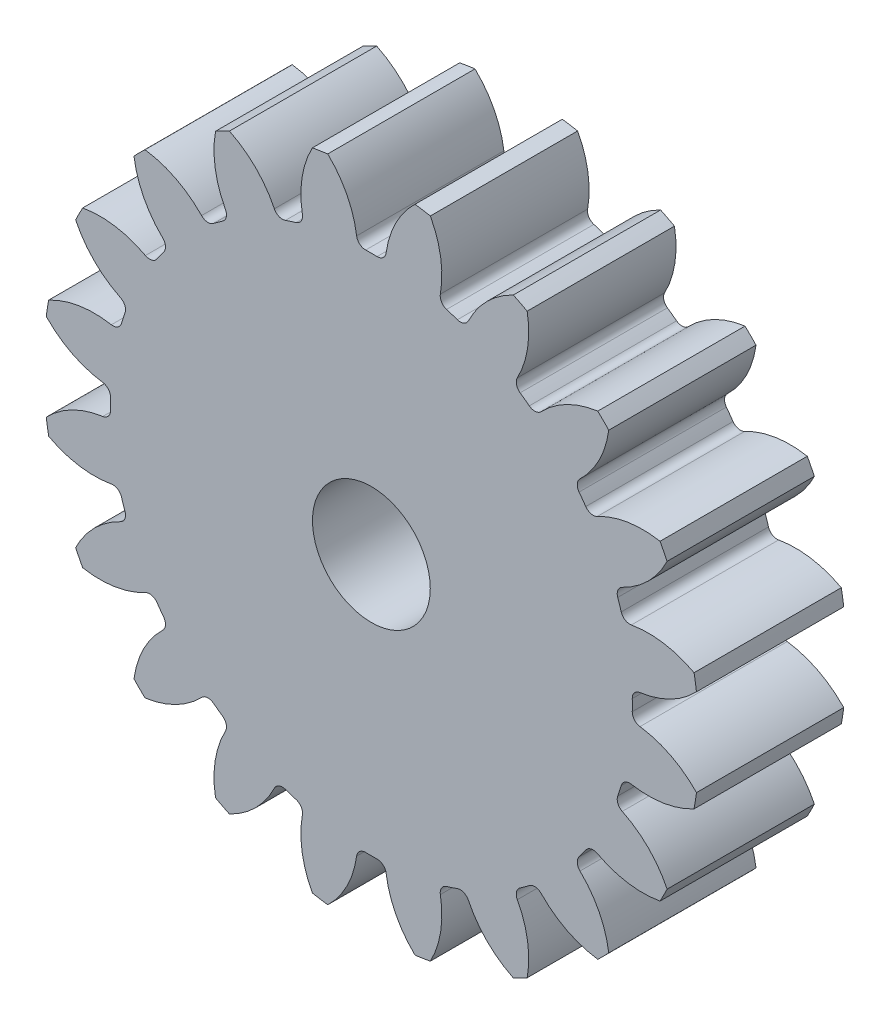
SolidWorks part; units mm, degrees
material "Custom Plastic"
ref_plane "Front Plane" through (0, 0, 0) normal (0, 0, 1) x (1, 0, 0)
ref_plane "Top Plane" through (0, 0, 0) normal (0, 1, 0) x (1, 0, 0)
ref_plane "Right Plane" through (0, 0, 0) normal (1, 0, 0) x (0, 0, -1)
sketch "Sketch1" plane through (0, 0, 0) normal (0, 0, 1) x (1, 0, 0)
  circle A0 centre (0, 0) radius 20.25
  circle A1 centre (0, 0) radius 22.275
  circle A2 centre (0, 0) radius 17.7188
  dimension "D1" = 40.5
  dimension "D3" = 35.4375
  dimension "D2" = 2.025
extrude "Boss-Extrude1" add sketch "Sketch1" along normal blind 10 contours A1
sketch "Sketch2" plane through (0, 0, 0) normal (0, 0, 1) x (1, 0, 0)
  line L0 (0, 0) -> (0, 22.275) construction
  line L1 (-1.5888, 20.1876) -> (1.5888, 20.1876) construction
  line L2 (-0.9484, 17.6934) -> (0, 0) construction
  line L3 (-2.3243, 22.3042) -> (0, 15.9182) construction
  line L4 (0, 0) -> (3.4846, 22.0008) construction
  line L5 (1.5888, 20.1876) -> (4.7273, 19.6905) construction
  circle A0 centre (0, 0) radius 22.275 construction
  arc A1 (-3.1037, 22.2092) -> (-0.9484, 17.6934) centre (-7.4915, 17.3426) cw
  arc A2 (3.1037, 22.2092) -> (0.9484, 17.6934) centre (7.4915, 17.3426) ccw
  circle A3 centre (0, 0) radius 17.7188 construction
  arc A4 (0.9484, 17.6934) -> (-0.9484, 17.6934) centre (0, 0) ccw
  circle A7 centre (0, 0) radius 20.25 construction
  circle A8 centre (0, 0) radius 22.425
  arc A9 (3.1037, 22.2092) -> (-3.1037, 22.2092) centre (0, 0) ccw
  circle A10 centre (0, 0) radius 22.275 construction
  point P0 (-3.1037, 22.3042)
  dimension "D2" = 20
  dimension "D3" = 9
  dimension "D1" = 0.15
extrude "Cut-Extrude1" cut sketch "Sketch2" along normal through all
fillet "Fillet1" radius 0.6075 2 edges at (0.9484, 17.6934, 5) (-0.9484, 17.6934, 5)
pattern_circular "CirPattern5" count 20 over 360 about axis through (0, 0, 0) along (0, 0, 1) of "Cut-Extrude1", "Fillet1"
sketch "Sketch3" plane through (0, 0, 10) normal (0, 0, 1) x (1, 0, 0)
  circle A0 centre (0, 0) radius 4
  dimension "D1" = 8
extrude "Cut-Extrude5" cut sketch "Sketch3" against normal through all
equation "\"Reference Diameter\"= 40.5mm"
equation "\"Pressure Angle\"= 20'Degrees"
equation "\"number of teeth\" = 20"
equation "\"module\"= \"Reference Diameter\" / \"number of teeth\""
equation "\"base diameter\"= \"Reference Diameter\" * cos ( \"Pressure Angle\" )"
equation "\"addendum\"= \"module\""
equation "\"tooth depth\"= 2.25 * \"module\""
equation "\"tip diameter\"= \"Reference Diameter\" + 2 * \"module\""
equation "\"root diameter\"= \"Reference Diameter\" - 2.5 * \"module\""
equation "\"D1@Sketch1\"=\"Reference Diameter\""
equation "\"D2@Sketch1\"=\"addendum\""
equation "\"D3@Sketch1\"=\"root diameter\""
equation "\"D1@Fillet1\"=0.3 * \"module\""
equation "\"D2@Sketch2\"=\"Pressure Angle\""
equation "\"D3@Sketch2\"=180 / \"number of teeth\""
